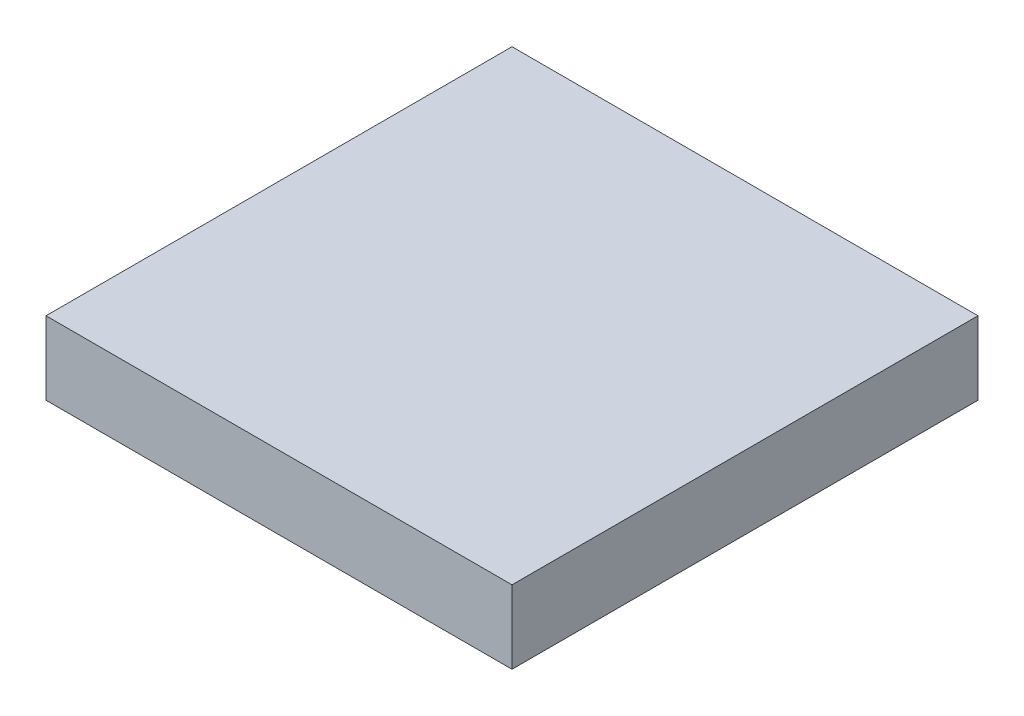
SolidWorks part; units mm, degrees
ref_plane "Front Plane" through (0, 0, 0) normal (0, 0, 1) x (1, 0, 0)
ref_plane "Top Plane" through (0, 0, 0) normal (0, 1, 0) x (1, 0, 0)
ref_plane "Right Plane" through (0, 0, 0) normal (1, 0, 0) x (0, 0, -1)
sketch "Sketch1" plane through (0, 0, 0) normal (0, 1, 0) x (1, 0, 0)
  line L1 (0, 0) -> (10, 0)
  line L2 (0, 0) -> (0, 10)
  line L3 (0, 10) -> (10, 10)
  line L4 (10, 0) -> (10, 10)
  dimension "D1" = 10
  dimension "D2" = 10
extrude "Boss-Extrude1" add sketch "Sketch1" along normal blind 1.57
sketch "Sketch2" plane through (0, 1.57, 0) normal (0, 1, 0) x (1, 0, 0)
  line L0 (10, 10) -> (0, 10) construction
  line L1 (0, 10) -> (0, 0) construction
  circle A0 centre (5, 5) radius 3
  point P2 (0, 0)
  point P3 (0, 0)
  point P6 (5, 10)
  point P9 (0, 5)
  dimension "D1" = 6
